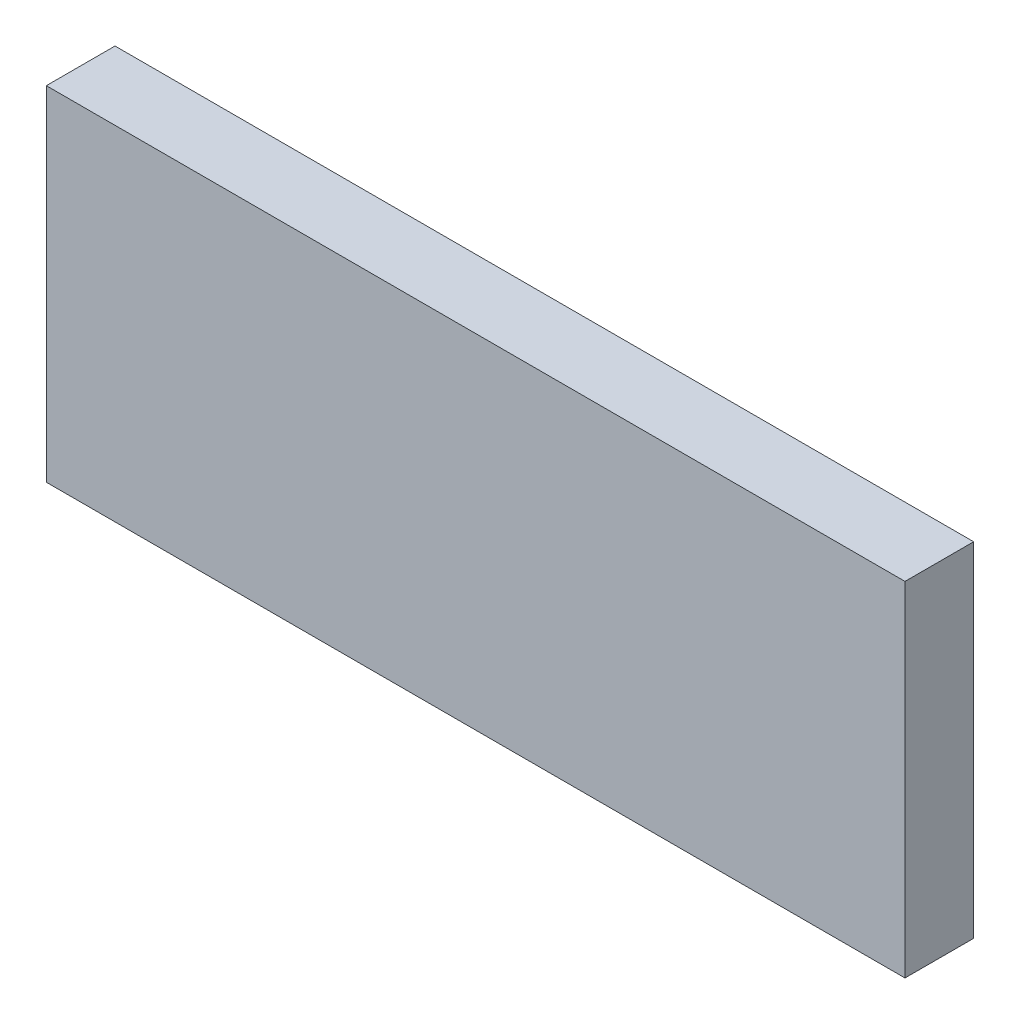
SolidWorks part; units mm, degrees
ref_plane "Спереди" through (0, 0, 0) normal (0, 0, 1) x (1, 0, 0)
ref_plane "Сверху" through (0, 0, 0) normal (0, 1, 0) x (1, 0, 0)
ref_plane "Справа" through (0, 0, 0) normal (1, 0, 0) x (0, 0, -1)
sketch "Эскиз1" plane through (0, 0, 0) normal (0, 0, 1) x (1, 0, 0)
  line L1 (0, 0) -> (625, 0)
  line L2 (0, 0) -> (0, 250)
  line L3 (0, 250) -> (625, 250)
  line L4 (625, 0) -> (625, 250)
extrude "Бобышка-Вытянуть1" add sketch "Эскиз1" along normal blind 50
